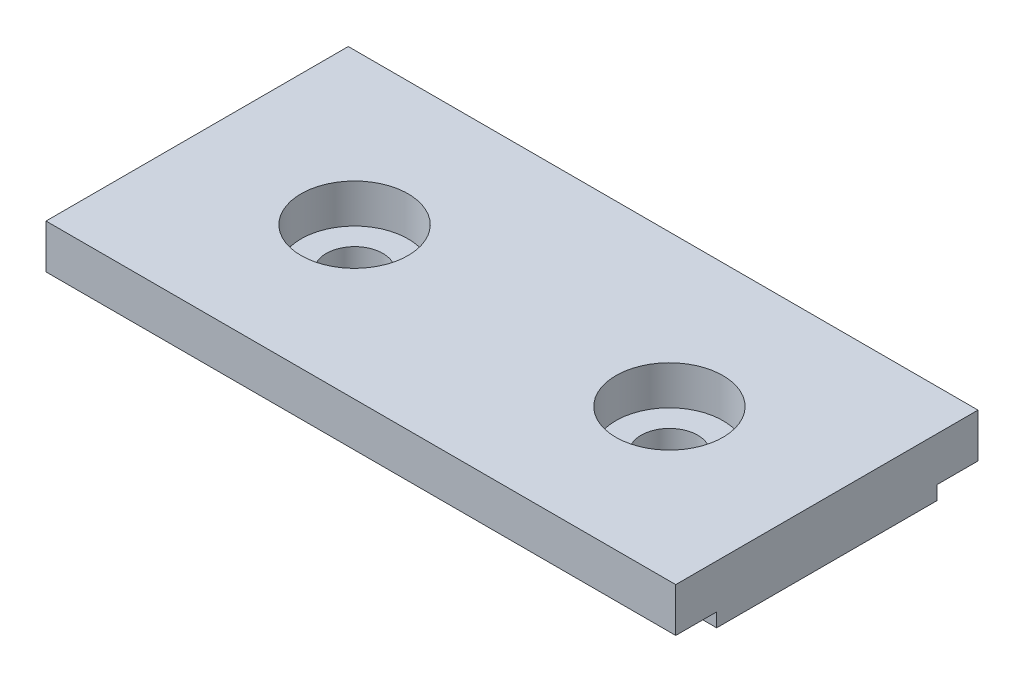
SolidWorks part; units mm, degrees
ref_plane "Plan de face" through (0, 0, 0) normal (0, 0, 1) x (1, 0, 0)
ref_plane "Plan de dessus" through (0, 0, 0) normal (0, 1, 0) x (1, 0, 0)
ref_plane "Plan de droite" through (0, 0, 0) normal (1, 0, 0) x (0, 0, -1)
sketch "Esquisse2" plane through (0, 0, 0) normal (1, 0, 0) x (0, 0, -1)
  line L0 (0, 9.0545) -> (0, -8.0364) construction
  line L1 (-12, 6.9455) -> (12, 6.9455)
  line L2 (12, 6.9455) -> (12, 3.4455)
  line L3 (12, 3.4455) -> (8.75, 3.4455)
  line L4 (8.75, 3.4455) -> (8.75, 2.3455)
  line L5 (8.75, 2.3455) -> (-8.75, 2.3455)
  line L6 (-8.75, 3.4455) -> (-8.75, 2.3455)
  line L7 (-12, 3.4455) -> (-8.75, 3.4455)
  line L8 (-12, 6.9455) -> (-12, 3.4455)
  point P10 (0, 2.3455)
  point P13 (0, 6.9455)
  dimension "D1" = 12
  dimension "D2" = 3.5
  dimension "D3" = 1.1
  dimension "D4" = 3.25
  dimension "D5" = 8.75
extrude "Boss.-Extru.1" add sketch "Esquisse2" along normal blind 50
sketch "Esquisse3" plane through (0, 6.9455, 0) normal (0, 1, 0) x (1, 0, 0)
  line L0 (-14.5984, 0) -> (69.7753, 0) construction
  line L1 (50, 12) -> (50, -12) construction
  point P3 (12.5, 0)
  point P5 (37.5, 0)
  dimension "D1" = 12.5
  dimension "D4" = 12.5
hole_wizard "Chambrage pour vis à tête hexagonale M42" positions "Esquisse3D2" profile "Esquisse5" counterbore size "M4" standard "Ansi Metric" end condition through all
sketch3d "Esquisse3D2"
  point P0 (12.5, 6.9455, 0)
  point P3 (37.5, 6.9455, 0)
sketch "Esquisse5" plane through (12.5, 6.9455, 0) normal (1, 0, 0) x (0, 0, 1)
  line L0 (0, 0) -> (0, 4.6)
  line L1 (0, 4.6) -> (2.25, 4.6)
  line L3 (2.25, 4.6) -> (2.25, 3.1)
  line L4 (2.25, 3.1) -> (4.25, 3.1)
  line L5 (4.25, 3.1) -> (4.25, 0)
  line L7 (4.25, 0) -> (0, 0)
  line L11 (0, -6.35) -> (0, 107.95) construction
  dimension "Diamètre du perçage jusqu'au prochain" = 4.5
  dimension "Profondeur du perçage jusqu'au prochain" = 4.6
  dimension "Diamètre du chambrage" = 8.5
  dimension "Profondeur du chambrage" = 3.1
